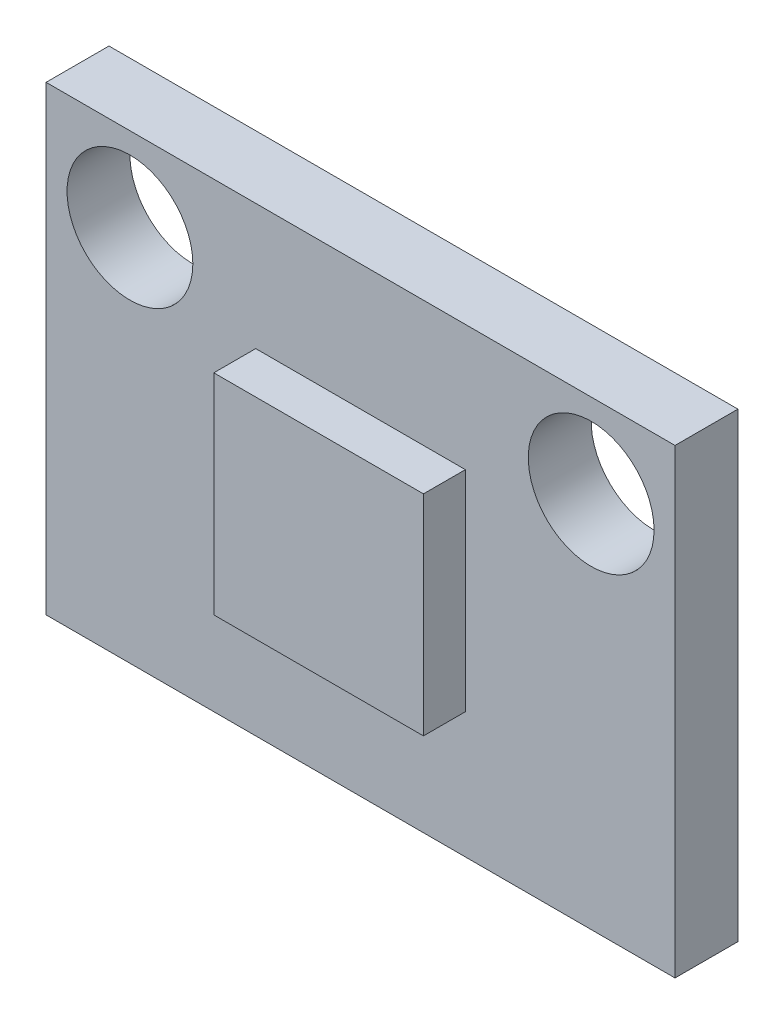
SolidWorks part; units mm, degrees
ref_plane "前视基准面" through (0, 0, 0) normal (0, 0, 1) x (1, 0, 0)
ref_plane "上视基准面" through (0, 0, 0) normal (0, 1, 0) x (1, 0, 0)
ref_plane "右视基准面" through (0, 0, 0) normal (1, 0, 0) x (0, 0, -1)
sketch "草图1" plane through (0, 0, 0) normal (0, 0, 1) x (1, 0, 0)
  line L1 (7.5, -5.5) -> (-7.5, -5.5)
  line L2 (7.5, -5.5) -> (7.5, 5.5)
  line L3 (7.5, 5.5) -> (-7.5, 5.5)
  line L4 (-7.5, -5.5) -> (-7.5, 5.5)
  line L5 (7.5, -5.5) -> (-7.5, 5.5) construction
  line L6 (7.5, 5.5) -> (-7.5, -5.5) construction
  circle A0 centre (-5.5, 3.5) radius 1.5
  circle A1 centre (5.5, 3.5) radius 1.5
  point P0 (0, 0)
  dimension "D3" = 3
  dimension "D4" = 3
  dimension "D5" = 2
  dimension "D6" = 2
  dimension "D7" = 2
  dimension "D8" = 2
  dimension "D1" = 15
  dimension "D2" = 11
extrude "凸台-拉伸1" add sketch "草图1" along normal blind 1.5
sketch "草图2" plane through (0, 0, 1.5) normal (0, 0, 1) x (1, 0, 0)
  line L1 (2.5, -2.5) -> (-2.5, -2.5)
  line L2 (2.5, -2.5) -> (2.5, 2.5)
  line L3 (2.5, 2.5) -> (-2.5, 2.5)
  line L4 (-2.5, -2.5) -> (-2.5, 2.5)
  line L5 (2.5, -2.5) -> (-2.5, 2.5) construction
  line L6 (2.5, 2.5) -> (-2.5, -2.5) construction
  point P0 (0, 0)
  dimension "D1" = 5
  dimension "D2" = 5
extrude "凸台-拉伸2" add sketch "草图2" along normal blind 1
